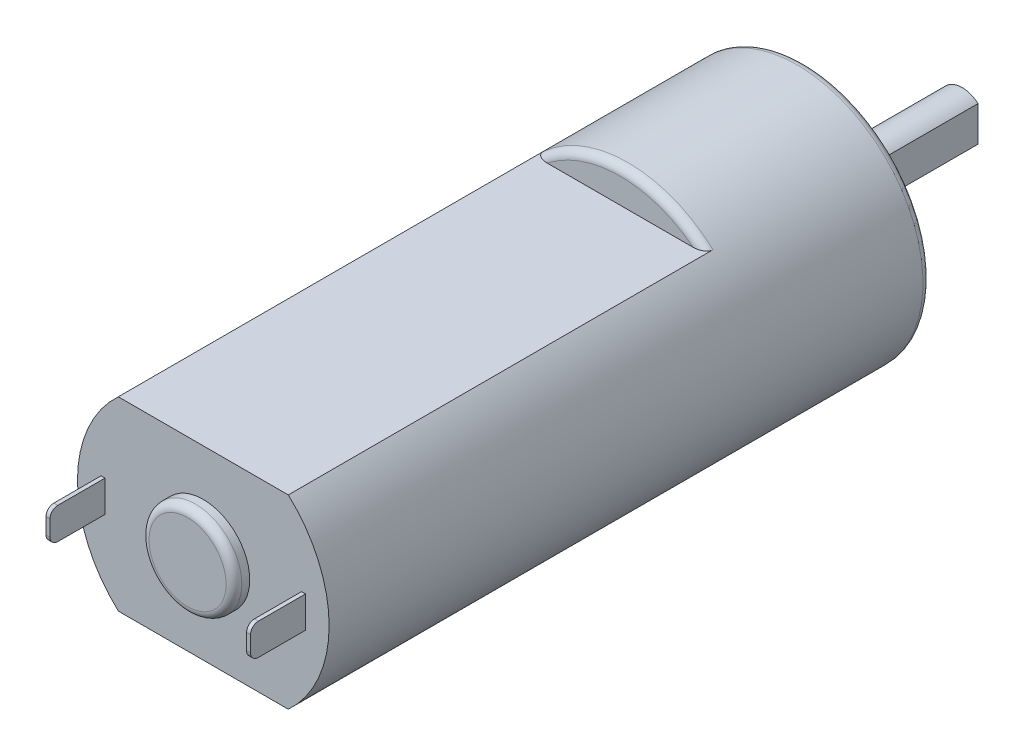
SolidWorks part; units mm, degrees
ref_plane "Front Plane" through (0, 0, 0) normal (0, 0, 1) x (1, 0, 0)
ref_plane "Top Plane" through (0, 0, 0) normal (0, 1, 0) x (1, 0, 0)
ref_plane "Right Plane" through (0, 0, 0) normal (1, 0, 0) x (0, 0, -1)
ref_plane "Plane1" through (0, 0, 0) normal (0, -1, 0) x (1, 0, 0)
sketch "Sketch1" plane through (0, 0, 0) normal (0, -1, 0) x (1, 0, 0)
  line L0 (8, 38.25) -> (0, 38.25)
  line L1 (0, 38.25) -> (0, 0)
  line L2 (0, 0) -> (8, 0)
  line L3 (8, 0) -> (8, 38.25)
  line L4 (0, 38.25) -> (0, 0) construction
revolve "Revolve1" add sketch "Sketch1" angle 360 about L4
sketch "Sketch2" plane through (0, 0, 0) normal (0, 0, -1) x (-1, 0, 0)
  circle A0 centre (0, 0) radius 3
extrude "Boss-Extrude1" add sketch "Sketch2" along normal blind 2
sketch "Sketch3" plane through (0, 0, -2) normal (0, 0, -1) x (-1, 0, 0)
  line L0 (-1, -1.118) -> (-1, 1.118)
  arc A0 (-1, 1.118) -> (-1, -1.118) centre (0, 0) cw
extrude "Boss-Extrude2" add sketch "Sketch3" along normal blind 8
sketch "Sketch4" plane through (0, 0, -2) normal (0, 0, -1) x (-1, 0, 0)
  line L0 (-1, -1.118) -> (-1, 1.118)
  arc A0 (-1, 1.118) -> (-1, -1.118) centre (0, 0) ccw
extrude "Cut-Extrude1" cut sketch "Sketch4" against normal blind 2
sketch "Sketch5" plane through (0, 0, 38.25) normal (0, 0, 1) x (1, 0, 0)
  line L0 (-5.4028, 5.9) -> (5.4028, 5.9)
  arc A0 (5.4028, 5.9) -> (-5.4028, 5.9) centre (0, 0) ccw
extrude "Cut-Extrude2" cut sketch "Sketch5" against normal blind 26.5
sketch "Sketch6" plane through (0, 0, 38.25) normal (0, 0, 1) x (1, 0, 0)
  line L0 (5.4028, -5.9) -> (-5.4028, -5.9)
  arc A0 (-5.4028, -5.9) -> (5.4028, -5.9) centre (0, 0) ccw
extrude "Cut-Extrude3" cut sketch "Sketch6" against normal blind 26.5
sketch "Sketch7" plane through (0, 0, 38.25) normal (0, 0, 1) x (1, 0, 0)
  line L0 (-6.5, 1) -> (-6.25, 1)
  line L1 (-6.25, 1) -> (-6.25, -1)
  line L2 (-6.25, -1) -> (-6.5, -1)
  line L3 (-6.5, -1) -> (-6.5, 1)
extrude "Boss-Extrude3" add sketch "Sketch7" along normal blind 3.5
sketch "Sketch8" plane through (0, 0, 38.25) normal (0, 0, 1) x (1, 0, 0)
  line L0 (6.25, 1) -> (6.5, 1)
  line L1 (6.5, 1) -> (6.5, -1)
  line L2 (6.5, -1) -> (6.25, -1)
  line L3 (6.25, -1) -> (6.25, 1)
extrude "Boss-Extrude4" add sketch "Sketch8" along normal blind 3.5
sketch "Sketch9" plane through (0, 0, 38.25) normal (0, 0, 1) x (1, 0, 0)
  circle A0 centre (0, 0) radius 2.95
extrude "Boss-Extrude5" add sketch "Sketch9" along normal blind 1
fillet "Fillet1" radius 0.5 8 edges at (-6.375, 1, 41.75) (6.375, 1, 41.75) (6.375, -1, 41.75) (0, -8, 11.75) (-6.375, -1, 41.75) (0, 8, 11.75) (-8, 0, 0) (2.95, 0, 39.25)
